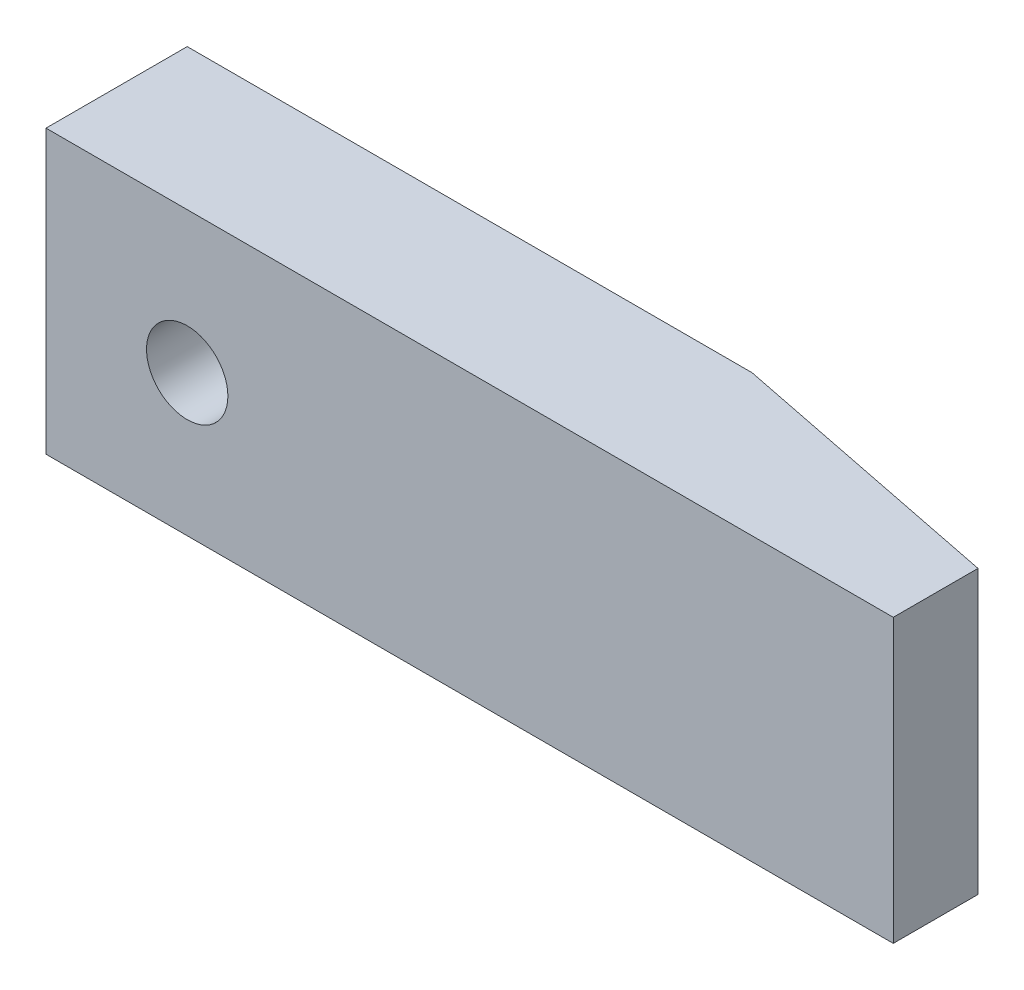
SolidWorks part; units mm, degrees
ref_plane "Front Plane" through (0, 0, 0) normal (1, 0, 0) x (0, 1, 0)
ref_plane "Top Plane" through (0, 0, 0) normal (0, 0, 1) x (0, 1, 0)
ref_plane "Right Plane" through (0, 0, 0) normal (0, 1, 0) x (-1, 0, 0)
sketch "Sketch1" plane through (0, 0, 0) normal (0, 1, 0) x (-1, 0, 0)
  line L1 (-19.05, -3.175) -> (19.05, -3.175)
  line L2 (-19.05, -3.175) -> (-19.05, 3.175)
  line L3 (-19.05, 3.175) -> (19.05, 3.175)
  line L4 (19.05, -3.175) -> (19.05, 3.175)
  line L5 (-19.05, -3.175) -> (19.05, 3.175) construction
  line L6 (-19.05, 3.175) -> (19.05, -3.175) construction
  point P0 (0, 0)
  dimension "D1" = 6.35
  dimension "D2" = 38.1
extrude "Boss-Extrude1" add sketch "Sketch1" along normal mid plane 12.7
hole_wizard "#27 (0.144) Diameter Hole1" positions "Sketch3" profile "Sketch4" hole size "#27" standard "ANSI Inch" end condition through all
sketch "Sketch3" plane through (0, 0, 3.175) normal (0, 0, 1) x (1, 0, 0)
  line L0 (-19.05, 6.35) -> (-19.05, -6.35) construction
  point P0 (-12.7, 0)
  dimension "D1" = 6.35
sketch "Sketch4" plane through (-12.7, 0, 3.175) normal (1, 0, 0) x (0, -1, 0)
  line L0 (0, 0) -> (0, 6.35)
  line L1 (0, 6.35) -> (1.8288, 6.35)
  line L2 (1.8288, 6.35) -> (1.8288, 0)
  line L5 (1.8288, 0) -> (0, 0)
  line L11 (0, -6.35) -> (0, 107.95) construction
  dimension "Thru Hole Dia." = 3.6576
  dimension "Thru Hole Depth" = 6.35
sketch "Sketch5" plane through (0, -6.35, 0) normal (0, -1, 0) x (1, 0, 0)
  line L0 (19.05, -0.635) -> (6.35, -3.175)
  line L1 (19.05, 3.175) -> (19.05, -3.175) construction
  line L2 (19.05, -3.175) -> (-19.05, -3.175) construction
  line L3 (6.35, -3.175) -> (19.05, -3.175)
  line L4 (19.05, -3.175) -> (19.05, -0.635)
  dimension "D1" = 12.7
  dimension "D2" = 2.54
extrude "Cut-Extrude1" cut sketch "Sketch5" against normal through all
